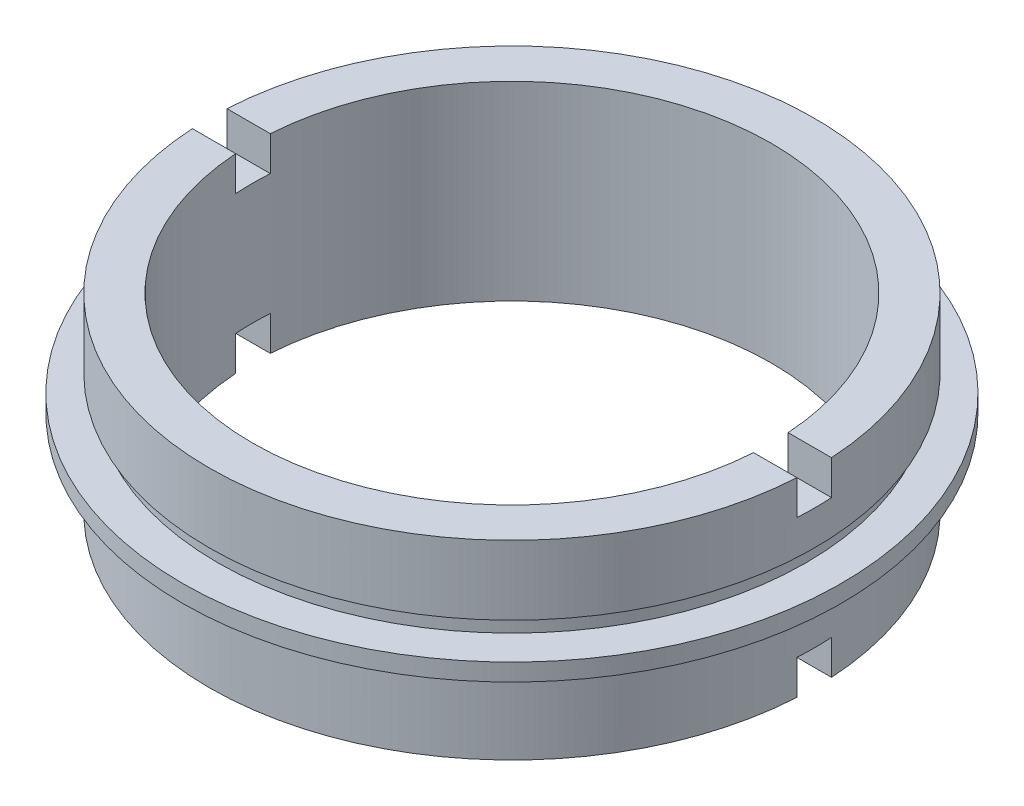
SolidWorks part; units mm, degrees
ref_plane "前视基准面" through (0, 0, 0) normal (0, 0, 1) x (1, 0, 0)
ref_plane "上视基准面" through (0, 0, 0) normal (0, 1, 0) x (1, 0, 0)
ref_plane "右视基准面" through (0, 0, 0) normal (1, 0, 0) x (0, 0, -1)
sketch "草图1" plane through (0, 0, 0) normal (0, 0, 1) x (1, 0, 0)
  line L0 (0, 22.6775) -> (0, 0) construction
  line L1 (-15, 11) -> (-17.5, 11)
  line L2 (-17.5, 11) -> (-17.5, 7)
  line L3 (-17.5, 7) -> (-17, 7)
  line L4 (-17, 7) -> (-17, 6)
  line L5 (-17, 6) -> (-19.05, 6)
  line L6 (-19.05, 6) -> (-19.05, 5)
  line L7 (-19.05, 5) -> (-17, 5)
  line L8 (-17, 5) -> (-17, 4)
  line L9 (-17, 4) -> (-17.5, 4)
  line L10 (-17.5, 4) -> (-17.5, 0)
  line L11 (-17.5, 0) -> (-15, 0)
  line L12 (-15, 0) -> (-15, 11)
  point P5 (-19.05, 5.5)
  dimension "D1" = 11
  dimension "D2" = 1
  dimension "D3" = 1
  dimension "D4" = 5
  dimension "D5" = 5
  dimension "D6" = 17.5
  dimension "D7" = 19.05
  dimension "D8" = 17.5
  dimension "D9" = 17
  dimension "D10" = 17
  dimension "D11" = 15
  dimension "D12" = 0
revolve "旋转1" add sketch "草图1" angle 360 about L0
cosmetic thread "装饰螺纹线1" parameters "D2"=34
cosmetic thread "装饰螺纹线2" parameters "D2"=34
cosmetic thread "装饰螺纹线3" parameters "D2"=31
sketch "草图2" plane through (0, 0, 0) normal (1, 0, 0) x (0, 0, -1)
  line L0 (15, 11) -> (-15, 11) construction
  line L1 (-1, 13.594) -> (1, 13.594)
  line L2 (-1, 13.594) -> (-1, 9)
  line L3 (-1, 9) -> (1, 9)
  line L4 (1, 13.594) -> (1, 9)
  line L5 (-1, 2) -> (1, 2)
  line L6 (-1, 2) -> (-1, -4.6679)
  line L7 (-1, -4.6679) -> (1, -4.6679)
  line L8 (1, 2) -> (1, -4.6679)
  dimension "D1" = 2
  dimension "D2" = 1
  dimension "D3" = 2
  dimension "D4" = 1
  dimension "D5" = 2
  dimension "D6" = 2
extrude "切除-拉伸1" cut sketch "草图2" against normal mid plane 79
